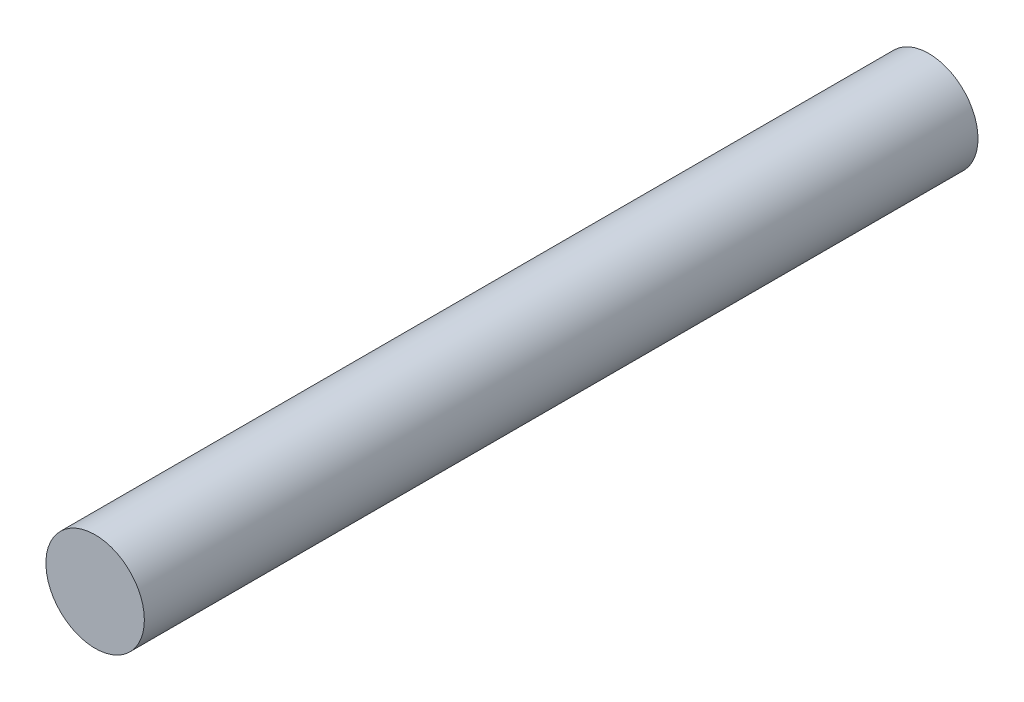
SolidWorks part; units mm, degrees
material "Default"
ref_plane "Top" through (0, 0, 0) normal (0, 0, 1) x (1, 0, 0)
ref_plane "Right" through (0, 0, 0) normal (0, 1, 0) x (1, 0, 0)
ref_plane "Front" through (0, 0, 0) normal (1, 0, 0) x (0, 0, -1)
sketch "Sketch3" plane through (0, 0, 0) normal (0, 0, 1) x (1, 0, 0)
  circle A0 centre (-18.1528, -99.414) radius 1.95
  circle A1 centre (-18.1528, -99.414) radius 2 construction
  dimension "D1" = 3.9
extrude "Boss-Extrude1" add sketch "Sketch3" against normal blind 33.02
